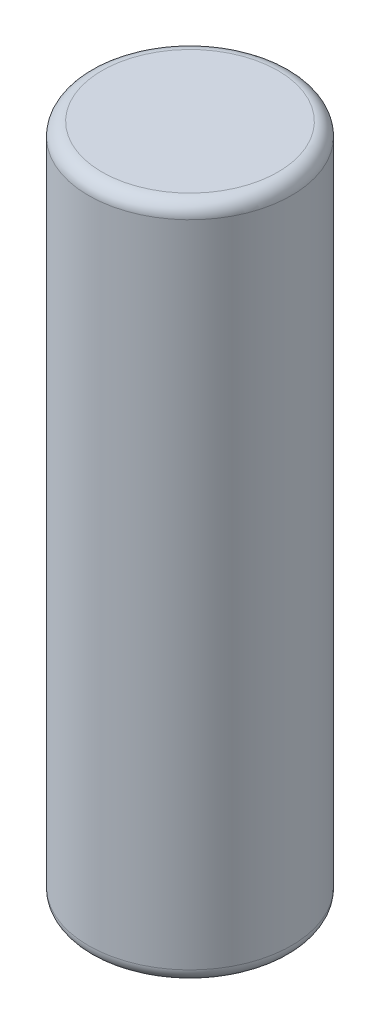
SolidWorks part; units mm, degrees
material "Alliage de magnésium"
ref_plane "Plan de face" through (0, 0, 0) normal (0, 0, 1) x (1, 0, 0)
ref_plane "Plan de dessus" through (0, 0, 0) normal (0, 1, 0) x (1, 0, 0)
ref_plane "Plan de droite" through (0, 0, 0) normal (1, 0, 0) x (0, 0, -1)
sketch "Esquisse1" plane through (0, 0, 0) normal (0, 1, 0) x (1, 0, 0)
  circle A0 centre (0, 0) radius 1.5
  dimension "D1" = 3
extrude "Boss.-Extru.1" add sketch "Esquisse1" along normal blind 10
fillet "Congé1" radius 0.2 2 edges at (0, 0, 1.5) (0, 10, 1.5)
